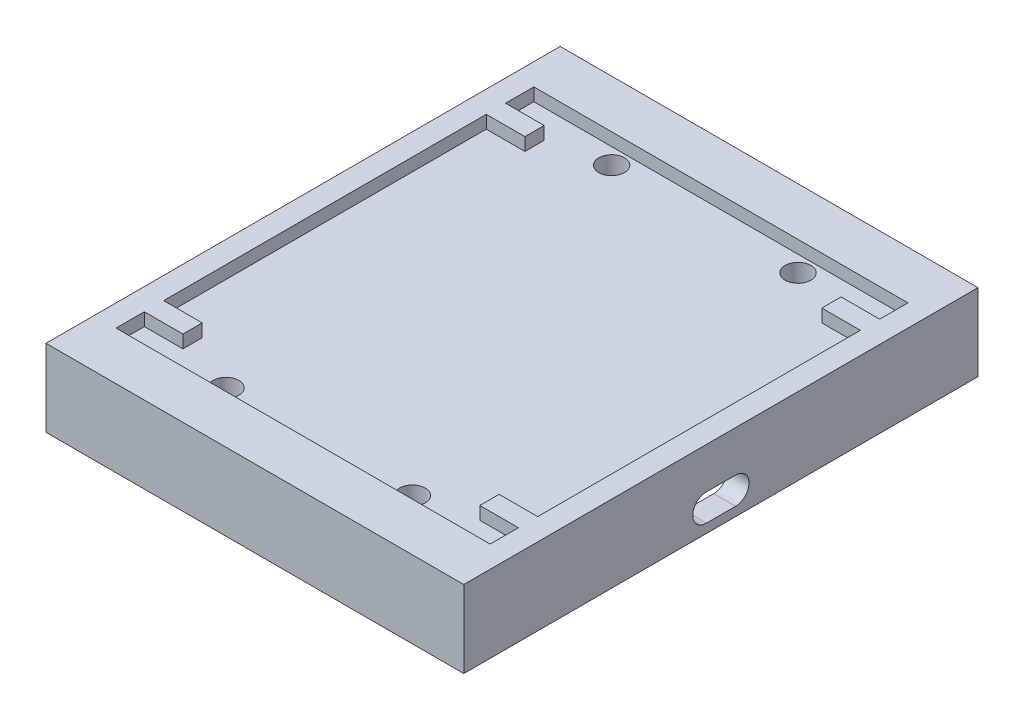
SolidWorks part; units mm, degrees
ref_plane "Front Plane" through (0, 0, 0) normal (0, 0, 1) x (1, 0, 0)
ref_plane "Top Plane" through (0, 0, 0) normal (0, 1, 0) x (1, 0, 0)
ref_plane "Right Plane" through (0, 0, 0) normal (1, 0, 0) x (0, 0, -1)
sketch "Sketch1" plane through (0, 0, 0) normal (0, 1, 0) x (1, 0, 0)
  line L0 (0, 0) -> (50.3642, 0) construction
  line L1 (-32.5, 40) -> (32.5, 40)
  line L2 (-32.5, 40) -> (-32.5, -40)
  line L3 (-32.5, -40) -> (32.5, -40)
  line L4 (32.5, 40) -> (32.5, -40)
  line L5 (-32.5, 40) -> (32.5, -40) construction
  line L6 (-32.5, -40) -> (32.5, 40) construction
  line L7 (50.3642, 0) -> (-57.9543, 0) construction
  point P0 (0, 0)
  dimension "D1" = 80
  dimension "D2" = 65
extrude "Boss-Extrude1" add sketch "Sketch1" along normal blind 12 contours L4 L3 L2 L1
sketch "Sketch3" plane through (0, 12, 0) normal (0, 1, 0) x (1, 0, 0)
  line L1 (-29.1, 32.5) -> (29.1, 32.5)
  line L2 (-29.1, 32.5) -> (-29.1, -32.5)
  line L3 (-29.1, -32.5) -> (29.1, -32.5)
  line L4 (29.1, 32.5) -> (29.1, -32.5)
  line L5 (-29.1, 32.5) -> (29.1, -32.5) construction
  line L6 (-29.1, -32.5) -> (29.1, 32.5) construction
  point P0 (0, 0)
  dimension "D1" = 65
  dimension "D2" = 58.2
extrude "Cut-Extrude4" cut sketch "Sketch3" against normal blind 2
sketch "Sketch6" plane through (0, 10, 0) normal (0, 1, 0) x (1, 0, 0)
  line L0 (0, -42.9236) -> (0, 40) construction
  line L1 (-32.5, 40) -> (32.5, 40) construction
  line L2 (29.1, 0) -> (-29.1, 0) construction
  line L5 (29.1, -32.5) -> (29.1, 32.5) construction
  line L6 (-29.1, 32.5) -> (-29.1, -32.5) construction
  circle A0 centre (14.5, 30) radius 2
  circle A1 centre (-14.5, 30) radius 2
  circle A2 centre (-14.5, -30) radius 2
  circle A3 centre (14.5, -30) radius 2
  dimension "D1" = 4
extrude "Cut-Extrude5" cut sketch "Sketch6" against normal blind 10
sketch "Sketch7" plane through (0, 0, 0) normal (0, 1, 0) x (1, 0, 0)
  line L1 (-29.1, 32.5) -> (29.1, 32.5)
  line L2 (-29.1, 32.5) -> (-29.1, -32.5)
  line L3 (-29.1, -32.5) -> (29.1, -32.5)
  line L4 (29.1, 32.5) -> (29.1, -32.5)
  line L5 (-29.1, 32.5) -> (29.1, -32.5) construction
  line L6 (-29.1, -32.5) -> (29.1, 32.5) construction
  point P0 (0, 0)
extrude "Cut-Extrude6" cut sketch "Sketch7" along normal blind 7
sketch "Sketch10" plane through (29.1, 0, 0) normal (-1, 0, 0) x (0, 0, 1)
  line L0 (0, 14.1687) -> (0, -11.7705) construction
  line L1 (32.5, 3.5) -> (-32.5, 3.5) construction
  line L2 (32.5, 7) -> (32.5, 0) construction
  line L3 (-32.5, 7) -> (-32.5, 0) construction
  line L4 (-2.2777, 3.5) -> (2.2777, 3.5) construction
  line L5 (-2.2777, 5.6014) -> (2.2777, 5.6014)
  line L6 (-2.2777, 1.3986) -> (2.2777, 1.3986)
  arc A0 (-2.2777, 5.6014) -> (-2.2777, 1.3986) centre (-2.2777, 3.5) ccw
  arc A1 (2.2777, 1.3986) -> (2.2777, 5.6014) centre (2.2777, 3.5) ccw
  point P10 (0, 3.5)
extrude "Cut-Extrude8" cut sketch "Sketch10" against normal blind 6
sketch "Sketch11" plane through (29.1, 0, 0) normal (-1, 0, 0) x (0, 0, 1)
  line L0 (0, 10) -> (0, 24.9453) construction
  line L1 (32.5, 10) -> (-32.5, 10) construction
  line L2 (0, 24.9453) -> (0, -12.6666) construction
  line L3 (32.5, 11) -> (-32.5, 11) construction
  line L4 (32.5, 10) -> (32.5, 12) construction
  line L5 (-32.5, 10) -> (-32.5, 12) construction
  line L7 (-25.1, 12) -> (-28.1, 12)
  line L8 (-25.1, 12) -> (-25.1, 10)
  line L9 (-25.1, 10) -> (-28.1, 10)
  line L10 (-28.1, 12) -> (-28.1, 10)
  line L11 (-25.1, 12) -> (-28.1, 10) construction
  line L12 (-25.1, 10) -> (-28.1, 12) construction
  line L13 (25.1, 10) -> (28.1, 10)
  line L14 (28.1, 12) -> (28.1, 10)
  line L15 (25.1, 12) -> (25.1, 10)
  line L16 (25.1, 12) -> (28.1, 12)
  point P12 (-26.6, 11)
  dimension "D1" = 26.6
  dimension "D2" = 3
extrude "Boss-Extrude3" add sketch "Sketch11" along normal blind 6
sketch "Sketch13" plane through (-29.1, 0, 0) normal (1, 0, 0) x (0, 0, -1)
  line L0 (0, 10) -> (0, 19.4178) construction
  line L1 (32.5, 10) -> (-32.5, 10) construction
  line L2 (32.5, 11) -> (-32.5, 11) construction
  line L3 (32.5, 10) -> (32.5, 12) construction
  line L4 (-32.5, 10) -> (-32.5, 12) construction
  line L5 (28.1, 10) -> (25.1, 10)
  line L6 (-28.1, 12) -> (-25.1, 12)
  line L7 (-28.1, 12) -> (-28.1, 10)
  line L8 (-28.1, 10) -> (-25.1, 10)
  line L9 (-25.1, 12) -> (-25.1, 10)
  line L10 (-28.1, 12) -> (-25.1, 10) construction
  line L11 (-28.1, 10) -> (-25.1, 12) construction
  line L12 (28.1, 12) -> (28.1, 10)
  line L13 (28.1, 12) -> (25.1, 12)
  line L14 (25.1, 12) -> (25.1, 10)
  point P11 (-26.6, 11)
  dimension "D1" = 26.6
  dimension "D2" = 3
extrude "Boss-Extrude4" add sketch "Sketch13" along normal blind 6
